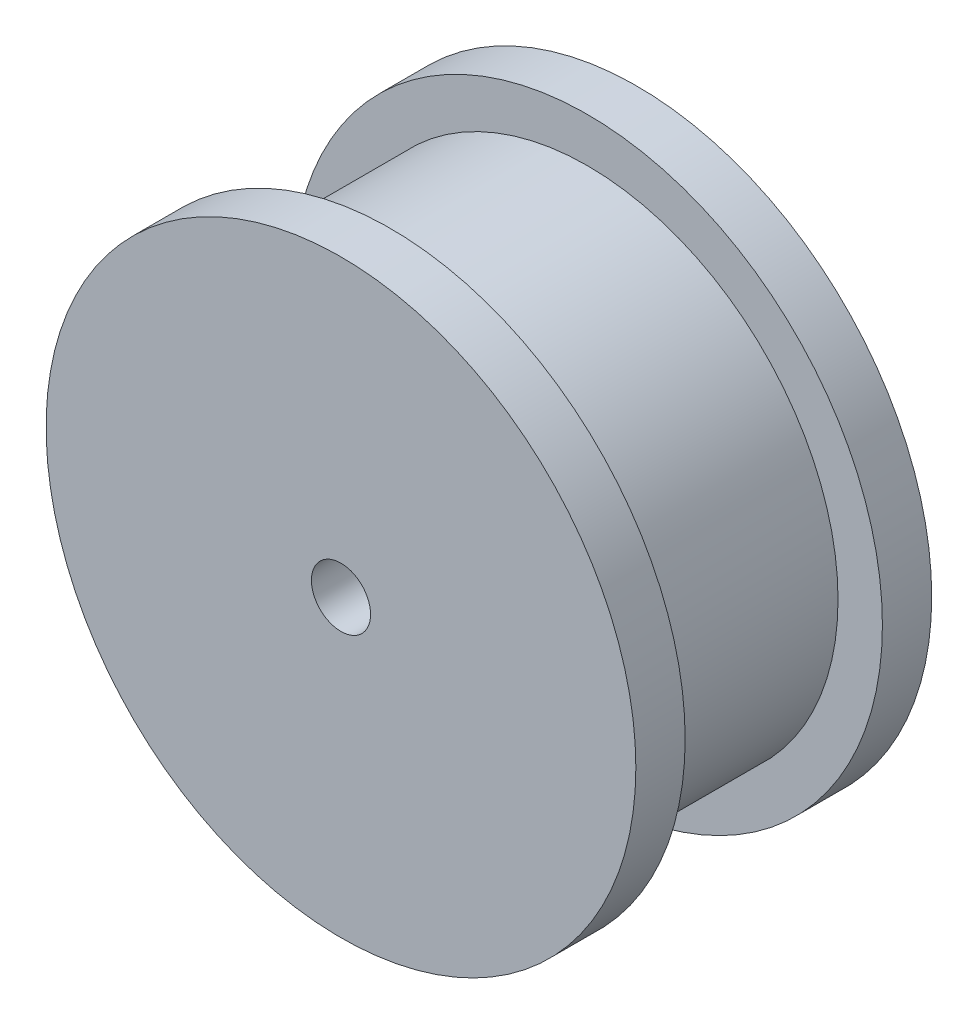
SolidWorks part; units mm, degrees
ref_plane "Front Plane" through (0, 0, 0) normal (0, 0, 1) x (1, 0, 0)
ref_plane "Top Plane" through (0, 0, 0) normal (0, 1, 0) x (1, 0, 0)
ref_plane "Right Plane" through (0, 0, 0) normal (1, 0, 0) x (0, 0, -1)
sketch "Sketch1" plane through (0, 0, 0) normal (0, 0, 1) x (1, 0, 0)
  circle A0 centre (0, 0) radius 25.4
  dimension "D1" = 50.8
extrude "Boss-Extrude1" add sketch "Sketch1" along normal mid plane 20
sketch "Sketch2" plane through (0, 0, 10) normal (0, 0, 1) x (1, 0, 0)
  circle A0 centre (0, 0) radius 25.4 construction
  circle A1 centre (0, 0) radius 25.4 construction
  circle A2 centre (0, 0) radius 29.9
  dimension "D1" = 4.5
extrude "Boss-Extrude2" add sketch "Sketch2" along normal blind 5
mirror "Mirror1" about plane through (0, 0, 0) normal (0, 0, 1) of "Boss-Extrude2"
sketch "Sketch3" plane through (0, 0, 15) normal (0, 0, 1) x (1, 0, 0)
  circle A0 centre (0, 0) radius 3
  dimension "D1" = 6
extrude "Cut-Extrude1" cut sketch "Sketch3" against normal blind 76.628
